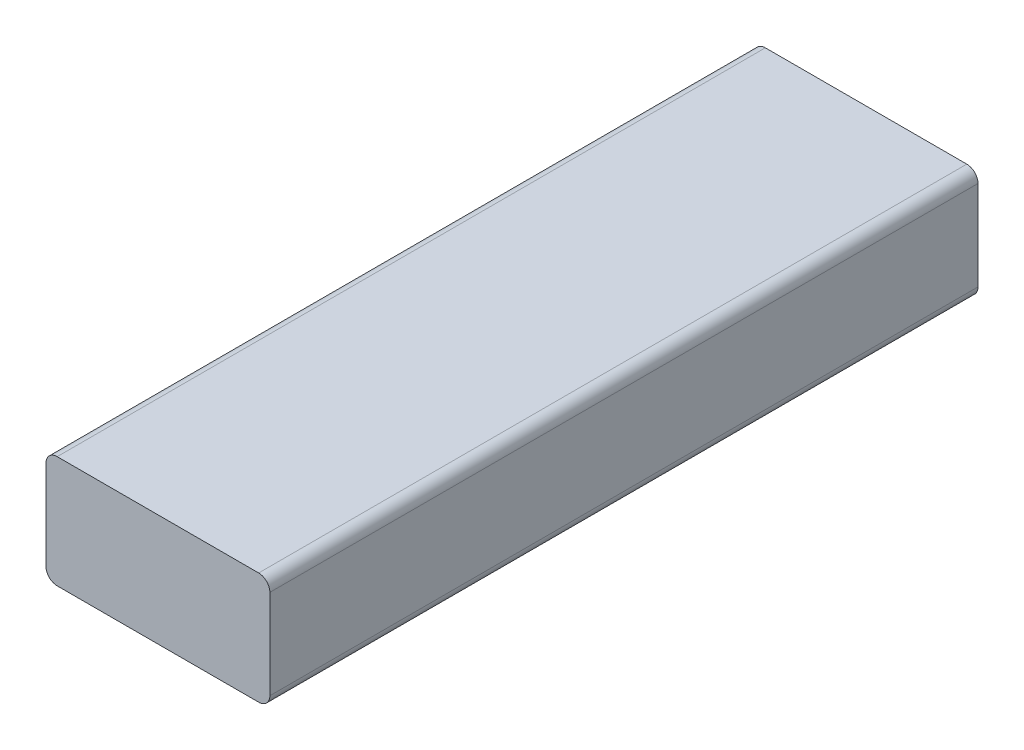
SolidWorks part; units mm, degrees
material "Balsa"
ref_plane "Front Plane" through (0, 0, 0) normal (0, 0, 1) x (1, 0, 0)
ref_plane "Top Plane" through (0, 0, 0) normal (0, 1, 0) x (1, 0, 0)
ref_plane "Right Plane" through (0, 0, 0) normal (1, 0, 0) x (0, 0, -1)
sketch "Sketch1" plane through (0, -12.7, 0) normal (0, -1, 0) x (-1, 0, 0)
  line L0 (-1812.7, 275) -> (-1812.7, -275) construction
  line L1 (-1914.3, 160.7) -> (-1812.7, 160.7)
  line L2 (-1914.3, 160.7) -> (-1914.3, -160.7)
  line L3 (-1914.3, -160.7) -> (-1812.7, -160.7)
  line L4 (-1812.7, 160.7) -> (-1812.7, -160.7)
  line L5 (-1812.7, 160.7) -> (-2587.3, 160.7) construction
  line L6 (-2587.3, -160.7) -> (-1812.7, -160.7) construction
  dimension "D1" = 101.6
extrude "Boss-Extrude1" add sketch "Sketch1" against normal blind 50.8
fillet "Fillet1" radius 5.08 4 edges at (1812.7, -12.7, 0) (1914.3, -12.7, 0) (1812.7, 38.1, 0) (1914.3, 38.1, 0)
